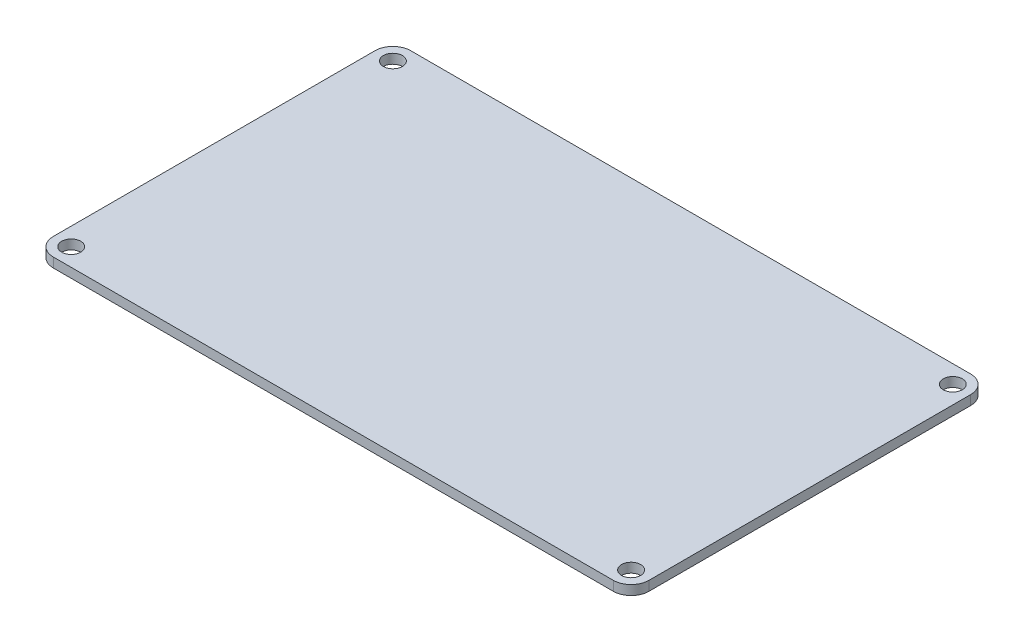
SolidWorks part; units mm, degrees
ref_plane "前视基准面" through (0, 0, 0) normal (0, 0, 1) x (1, 0, 0)
ref_plane "上视基准面" through (0, 0, 0) normal (0, 1, 0) x (1, 0, 0)
ref_plane "右视基准面" through (0, 0, 0) normal (1, 0, 0) x (0, 0, -1)
sketch "草图1" plane through (0, 0, 0) normal (0, 1, 0) x (1, 0, 0)
  line L1 (-50, 30) -> (50, 30)
  line L2 (-50, 30) -> (-50, -30)
  line L3 (-50, -30) -> (50, -30)
  line L4 (50, 30) -> (50, -30)
  line L5 (-50, 30) -> (50, -30) construction
  line L6 (-50, -30) -> (50, 30) construction
  point P0 (0, 0)
  dimension "D1" = 100
  dimension "D2" = 60
extrude "凸台-拉伸1" add sketch "草图1" along normal blind 1.6
sketch "草图2" plane through (0, 1.6, 0) normal (0, 1, 0) x (1, 0, 0)
  line L0 (0, 11.4648) -> (0, -11.1115) construction
  line L1 (-16.7682, 0) -> (14.1439, 0) construction
  line L2 (-50, 30) -> (50, 30) construction
  line L3 (-50, 30) -> (-50, -30) construction
  circle A0 centre (-47, 27) radius 1.6
  circle A1 centre (47, 27) radius 1.6
  circle A2 centre (47, -27) radius 1.6
  circle A3 centre (-47, -27) radius 1.6
  point P7 (-43.8597, 23.3897)
  dimension "D1" = 3.2
  dimension "D2" = 3
  dimension "D3" = 3
extrude "切除-拉伸1" cut sketch "草图2" against normal through all
fillet "圆角1" radius 3 4 edges at (50, 0.8, -30) (50, 0.8, 30) (-50, 0.8, 30) (-50, 0.8, -30)
